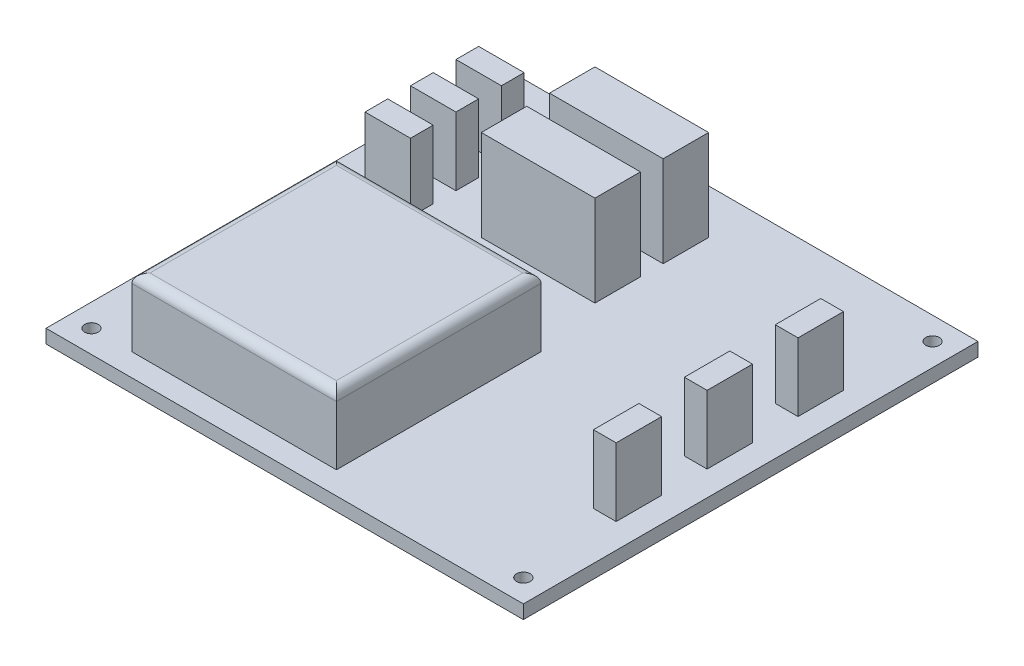
SolidWorks part; units mm, degrees
ref_plane "Face" through (0, 0, 0) normal (0, 0, 1) x (1, 0, 0)
ref_plane "Dessus" through (0, 0, 0) normal (0, 1, 0) x (1, 0, 0)
ref_plane "Droite" through (0, 0, 0) normal (1, 0, 0) x (0, 0, -1)
sketch "Esquisse1" plane through (0, 0, 0) normal (0, 1, 0) x (1, 0, 0)
  line L0 (52.5, 100) -> (52.5, 0) construction
  line L1 (0, 0) -> (105, 0)
  line L2 (0, 0) -> (0, 100)
  line L3 (0, 100) -> (105, 100)
  line L4 (105, 0) -> (105, 100)
  line L5 (0, 50) -> (105, 50) construction
  circle A0 centre (5, 95) radius 1.5
  circle A1 centre (100, 95) radius 1.5
  circle A2 centre (100, 5) radius 1.5
  circle A3 centre (5, 5) radius 1.5
  dimension "D3" = 3
  dimension "D1" = 105
  dimension "D2" = 100
  dimension "D4" = 5
  dimension "D5" = 5
extrude "Extrusion1" add sketch "Esquisse1" along normal blind 3
sketch "Esquisse2" plane through (0, 3, 0) normal (0, 1, 0) x (1, 0, 0)
  line L1 (13.9057, 4.9759) -> (58.9057, 4.9759)
  line L2 (13.9057, 4.9759) -> (13.9057, 49.9759)
  line L3 (13.9057, 49.9759) -> (58.9057, 49.9759)
  line L4 (58.9057, 4.9759) -> (58.9057, 49.9759)
  dimension "D1" = 45
extrude "Extrusion2" add sketch "Esquisse2" along normal blind 15
fillet "Congé1" radius 2 4 edges at (36.4057, 18, -49.9759) (58.9057, 18, -27.4759) (36.4057, 18, -4.9759) (13.9057, 18, -27.4759)
sketch "Esquisse3" plane through (0, 3, 0) normal (0, 1, 0) x (1, 0, 0)
  line L0 (94.5276, 75.8844) -> (99.5276, 75.8844)
  line L1 (8.8844, 86.2828) -> (18.8844, 86.2828)
  line L2 (8.8844, 86.2828) -> (8.8844, 81.2828)
  line L3 (8.8844, 81.2828) -> (18.8844, 81.2828)
  line L4 (18.8844, 86.2828) -> (18.8844, 81.2828)
  line L5 (8.8844, 76.2828) -> (18.8844, 76.2828)
  line L6 (8.8844, 76.2828) -> (8.8844, 71.2828)
  line L7 (8.8844, 71.2828) -> (18.8844, 71.2828)
  line L8 (18.8844, 76.2828) -> (18.8844, 71.2828)
  line L9 (8.8844, 66.2828) -> (18.8844, 66.2828)
  line L10 (8.8844, 66.2828) -> (8.8844, 61.2828)
  line L11 (8.8844, 61.2828) -> (18.8844, 61.2828)
  line L12 (18.8844, 66.2828) -> (18.8844, 61.2828)
  line L13 (94.5276, 75.8844) -> (94.5276, 65.8844)
  line L14 (94.5276, 65.8844) -> (99.5276, 65.8844)
  line L15 (99.5276, 75.8844) -> (99.5276, 65.8844)
  line L16 (94.5276, 55.8844) -> (99.5276, 55.8844)
  line L17 (94.5276, 55.8844) -> (94.5276, 45.8844)
  line L18 (94.5276, 45.8844) -> (99.5276, 45.8844)
  line L19 (99.5276, 55.8844) -> (99.5276, 45.8844)
  line L20 (94.5276, 35.8844) -> (99.5276, 35.8844)
  line L21 (94.5276, 35.8844) -> (94.5276, 25.8844)
  line L22 (94.5276, 25.8844) -> (99.5276, 25.8844)
  line L23 (99.5276, 35.8844) -> (99.5276, 25.8844)
  line L24 (8.8844, 86.2828) -> (8.8844, 61.2828) construction
  line L25 (99.5276, 75.8844) -> (99.5276, 25.8844) construction
  dimension "D1" = 5
  dimension "D2" = 10
  dimension "D3" = 5
  dimension "D4" = 5
  dimension "D5" = 10
  dimension "D6" = 5
  dimension "D7" = 10
  dimension "D8" = 10
extrude "Extrusion3" add sketch "Esquisse3" along normal blind 15
sketch "Esquisse4" plane through (0, 3, 0) normal (0, 1, 0) x (1, 0, 0)
  line L1 (30.5777, 90.1652) -> (55.5777, 90.1652)
  line L2 (30.5777, 90.1652) -> (30.5777, 80.1652)
  line L3 (30.5777, 80.1652) -> (55.5777, 80.1652)
  line L4 (55.5777, 90.1652) -> (55.5777, 80.1652)
  line L5 (30.5777, 75.1652) -> (55.5777, 75.1652)
  line L6 (30.5777, 75.1652) -> (30.5777, 65.1652)
  line L7 (30.5777, 65.1652) -> (55.5777, 65.1652)
  line L8 (55.5777, 75.1652) -> (55.5777, 65.1652)
  dimension "D1" = 10
  dimension "D2" = 25
  dimension "D3" = 5
extrude "Extrusion4" add sketch "Esquisse4" along normal blind 20
